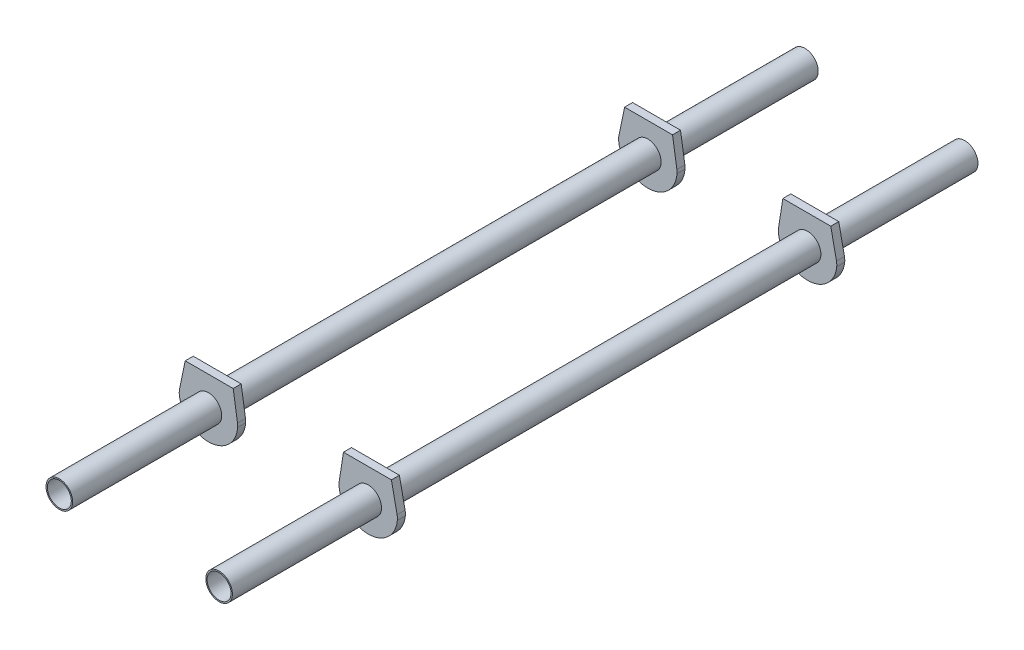
SolidWorks part; units mm, degrees
ref_plane "Piano frontale" through (0, 0, 0) normal (0, 0, 1) x (1, 0, 0)
ref_plane "Piano superiore" through (0, 0, 0) normal (0, 1, 0) x (1, 0, 0)
ref_plane "Piano destro" through (0, 0, 0) normal (1, 0, 0) x (0, 0, -1)
sketch "Schizzo1" plane through (0, 0, 0) normal (0, 0, 1) x (1, 0, 0)
  line L0 (55, 0) -> (-55, 0) construction
  circle A0 centre (30, 0) radius 5
  circle A1 centre (30, 0) radius 4.5
  point P2 (10.1112, -1.633)
  dimension "D1" = 10
  dimension "D2" = 9
  dimension "D3" = 30
extrude "Estrusione-Estrusione1" add sketch "Schizzo1" along normal mid plane 280
sketch "Schizzo2" plane through (0, 0, 0) normal (0, 0, 1) x (1, 0, 0)
  line L0 (19.0854, 0.5486) -> (20.712, 11)
  line L1 (20.712, 11) -> (38.712, 11)
  line L2 (38.712, 11) -> (40.8494, 0.7239)
  line L3 (30, 0) -> (30, 16.5351) construction
  circle A0 centre (30, 0) radius 5
  arc A1 (19.0308, -0.823) -> (40.9453, -1.0954) centre (30, 0) ccw
  circle A2 centre (30, 0) radius 4.5 construction
  circle A3 centre (30, 0) radius 5 construction
  arc A4 (19.0854, 0.5486) -> (19.0308, -0.823) centre (25.014, -0.3741) ccw
  arc A5 (40.8494, 0.7239) -> (40.9453, -1.0954) centre (34.9751, -0.4979) cw
  point P11 (0, 0)
  point P15 (19, 0)
  point P18 (41, 0)
  dimension "D1" = 18
  dimension "D2" = 22
  dimension "D3" = 6
  dimension "D4" = 6
extrude "Estrusione-Estrusione2" add sketch "Schizzo2" along direction (0, 0, 1) on the side of the normal mid plane 3 from offset 82.5
mirror "Specchia5" about plane through (0, 0, 0) normal (0, 0, 1) of bodies 104
mirror "Specchia9" about plane through (0, 0, 0) normal (1, 0, 0) of bodies 105
